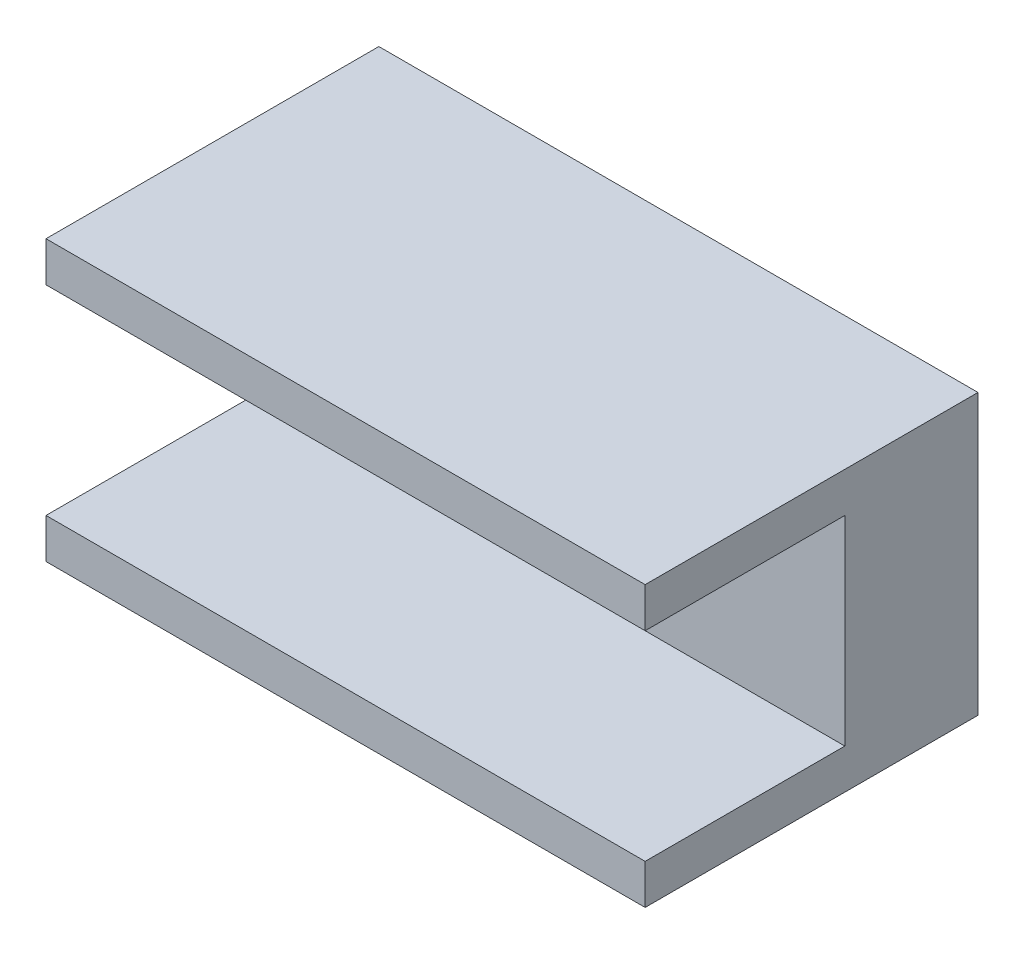
SolidWorks part; units mm, degrees
ref_plane "前视基准面" through (0, 0, 0) normal (0, 0, 1) x (1, 0, 0)
ref_plane "上视基准面" through (0, 0, 0) normal (0, 1, 0) x (1, 0, 0)
ref_plane "右视基准面" through (0, 0, 0) normal (1, 0, 0) x (0, 0, -1)
other "Configuration Table"
sketch "草图1" plane through (0, 0, 0) normal (0, 0, 1) x (1, 0, 0)
  line L1 (-143.3796, 418.8096) -> (-98.3796, 418.8096)
  line L2 (-143.3796, 418.8096) -> (-143.3796, 397.8096)
  line L3 (-143.3796, 397.8096) -> (-98.3796, 397.8096)
  line L4 (-98.3796, 418.8096) -> (-98.3796, 397.8096)
  dimension "D1" = 45
  dimension "D2" = 21
extrude "凸台-拉伸1" add sketch "草图1" along normal blind 25
sketch "草图2" plane through (0, 0, 25) normal (0, 0, 1) x (1, 0, 0)
  line L0 (-143.3796, 418.8096) -> (-143.3796, 397.8096) construction
  line L1 (-143.3796, 415.8096) -> (-98.3796, 415.8096)
  line L2 (-143.3796, 415.8096) -> (-143.3796, 400.8096)
  line L3 (-143.3796, 400.8096) -> (-98.3796, 400.8096)
  line L4 (-98.3796, 415.8096) -> (-98.3796, 400.8096)
  line L5 (-98.3796, 397.8096) -> (-98.3796, 418.8096) construction
  line L6 (-98.3796, 418.8096) -> (-143.3796, 418.8096) construction
  line L7 (-143.3796, 397.8096) -> (-98.3796, 397.8096) construction
  dimension "D1" = 3
  dimension "D2" = 3
extrude "切除-拉伸1" cut sketch "草图2" against normal blind 15
